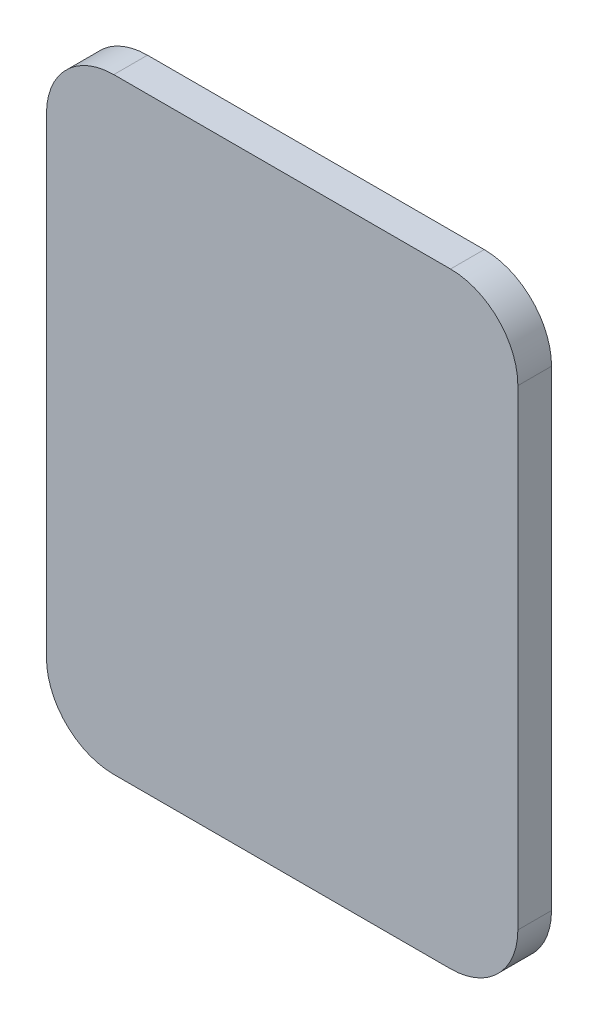
SolidWorks part; units mm, degrees
material "6061-T6 (SS)"
ref_plane "Front Plane" through (0, 0, 0) normal (0, 0, 1) x (1, 0, 0)
ref_plane "Top Plane" through (0, 0, 0) normal (0, 1, 0) x (1, 0, 0)
ref_plane "Right Plane" through (0, 0, 0) normal (1, 0, 0) x (0, 0, -1)
sketch "Sketch1" plane through (0, 0, 0) normal (0, 0, 1) x (1, 0, 0)
  line L1 (-35, 45) -> (35, 45)
  line L2 (-35, 45) -> (-35, -45)
  line L3 (-35, -45) -> (35, -45)
  line L4 (35, 45) -> (35, -45)
  line L5 (-35, 45) -> (35, -45) construction
  line L6 (-35, -45) -> (35, 45) construction
  point P0 (0, 0)
  dimension "D1" = 70
  dimension "D2" = 90
extrude "Boss-Extrude1" add sketch "Sketch1" along normal blind 5
sketch "Sketch3" plane through (0, 0, 0) normal (0, 0, -1) x (-1, 0, 0)
  line L0 (0, 36.7243) -> (0, -38.6187) construction
  line L1 (12.5, -25) -> (7.5, -25)
  line L2 (-12.5, 25) -> (-7.5, 25)
  line L3 (-12.5, 25) -> (-12.5, -25)
  line L4 (-12.5, -25) -> (-7.5, -25)
  line L5 (-7.5, 25) -> (-7.5, -25)
  line L6 (-12.5, 25) -> (-7.5, -25) construction
  line L7 (-12.5, -25) -> (-7.5, 25) construction
  line L8 (12.5, 25) -> (12.5, -25)
  line L9 (12.5, 25) -> (7.5, 25)
  line L10 (7.5, 25) -> (7.5, -25)
  point P3 (-10, 0)
  dimension "D1" = 5
  dimension "D2" = 50
  dimension "D3" = 10
extrude "Boss-Extrude2" add sketch "Sketch3" along normal blind 20
sketch "Sketch4" plane through (12.5, 0, 0) normal (1, 0, 0) x (0, 0, -1)
  line L0 (-18.5307, 0) -> (40.1987, 0) construction
  line L1 (20, 25) -> (20, -25) construction
  circle A0 centre (10, 12.5) radius 3
  circle A1 centre (10, -12.5) radius 3
  dimension "D3" = 6
  dimension "D1" = 12.5
  dimension "D2" = 10
extrude "Cut-Extrude1" cut sketch "Sketch4" against normal through all
fillet "Fillet1" radius 3 6 edges at (-10, 25, 0) (-12.5, 0, 0) (-10, -25, 0) (10, -25, 0) (10, 25, 0) (12.5, 0, 0)
fillet "Fillet2" radius 10 4 edges at (-10, 25, -20) (-10, -25, -20) (10, -25, -20) (10, 25, -20)
fillet "Fillet3" radius 10 4 edges at (-35, -45, 2.5) (35, -45, 2.5) (35, 45, 2.5) (-35, 45, 2.5)
